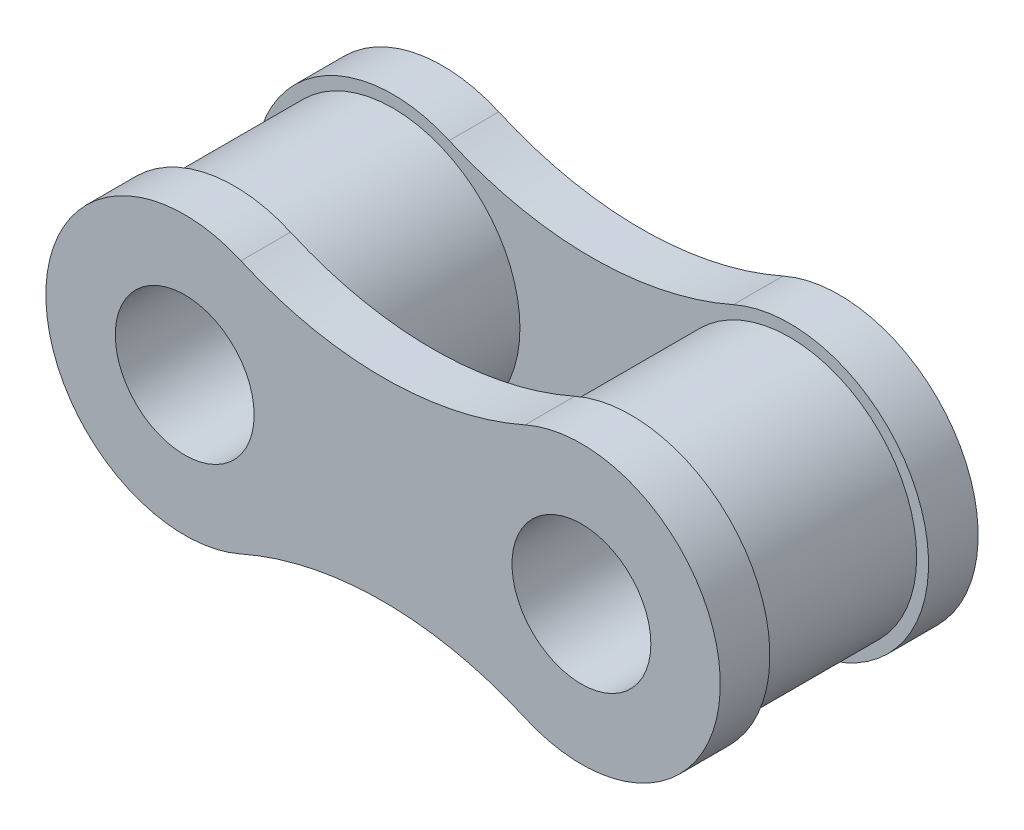
SolidWorks part; units mm, degrees
material "AISI 4130 Steel, normalized at 870C"
ref_plane "Front Plane" through (0, 0, 0) normal (0, 0, 1) x (1, 0, 0)
ref_plane "Top Plane" through (0, 0, 0) normal (0, 1, 0) x (1, 0, 0)
ref_plane "Right Plane" through (0, 0, 0) normal (1, 0, 0) x (0, 0, -1)
sketch "Sketch1" plane through (0, 0, 0) normal (0, 0, 1) x (1, 0, 0)
  circle A0 centre (0, 0) radius 5.08
  circle A1 centre (15.875, 0) radius 5.08
  circle A2 centre (0, 0) radius 3.81
  circle A3 centre (15.875, 0) radius 3.81
  dimension "D1" = 10.16
  dimension "D3" = 7.62
  dimension "D2" = 15.875
extrude "Boss-Extrude1" add sketch "Sketch1" along normal mid plane 6.35
sketch "Sketch2" plane through (0, 0, 3.175) normal (0, 0, 1) x (1, 0, 0)
  line L0 (0, 0) -> (6.5925, 0) construction
  line L1 (0, 5.08) -> (15.875, 5.08) construction
  arc A0 (2.2507, 5.08) -> (2.2507, -5.08) centre (0, 0) ccw
  arc A1 (13.6243, -5.08) -> (13.6243, 5.08) centre (15.875, 0) ccw
  circle A2 centre (0, 0) radius 2.7781
  circle A3 centre (15.875, 0) radius 2.7781
  arc A4 (2.2507, 5.08) -> (13.6243, 5.08) centre (7.9375, 17.9158) ccw
  circle A5 centre (0, 0) radius 5.08 construction
  circle A6 centre (15.875, 0) radius 5.08 construction
  arc A7 (2.2507, -5.08) -> (13.6243, -5.08) centre (7.9375, -17.9158) cw
  dimension "D1" = 11.1125
  dimension "D2" = 5.5562
extrude "Boss-Extrude2" add sketch "Sketch2" along normal blind 1.9844 separate body
mirror "Mirror1" about plane through (0, 0, 0) normal (0, 0, 1) of bodies 103 104
sketch "Sketch3" plane through (0, 0, -3.175) normal (0, 0, 1) x (1, 0, 0)
  circle A0 centre (0, 0) radius 2.7781
  circle A1 centre (0, 0) radius 2.7781 construction
  circle A2 centre (0, 0) radius 3.81
  circle A3 centre (0, 0) radius 3.81 construction
  circle A4 centre (15.875, 0) radius 2.7781
  circle A5 centre (15.875, 0) radius 3.81
extrude "Boss-Extrude3" add sketch "Sketch3" along normal up to next (8.3344 mm away)
